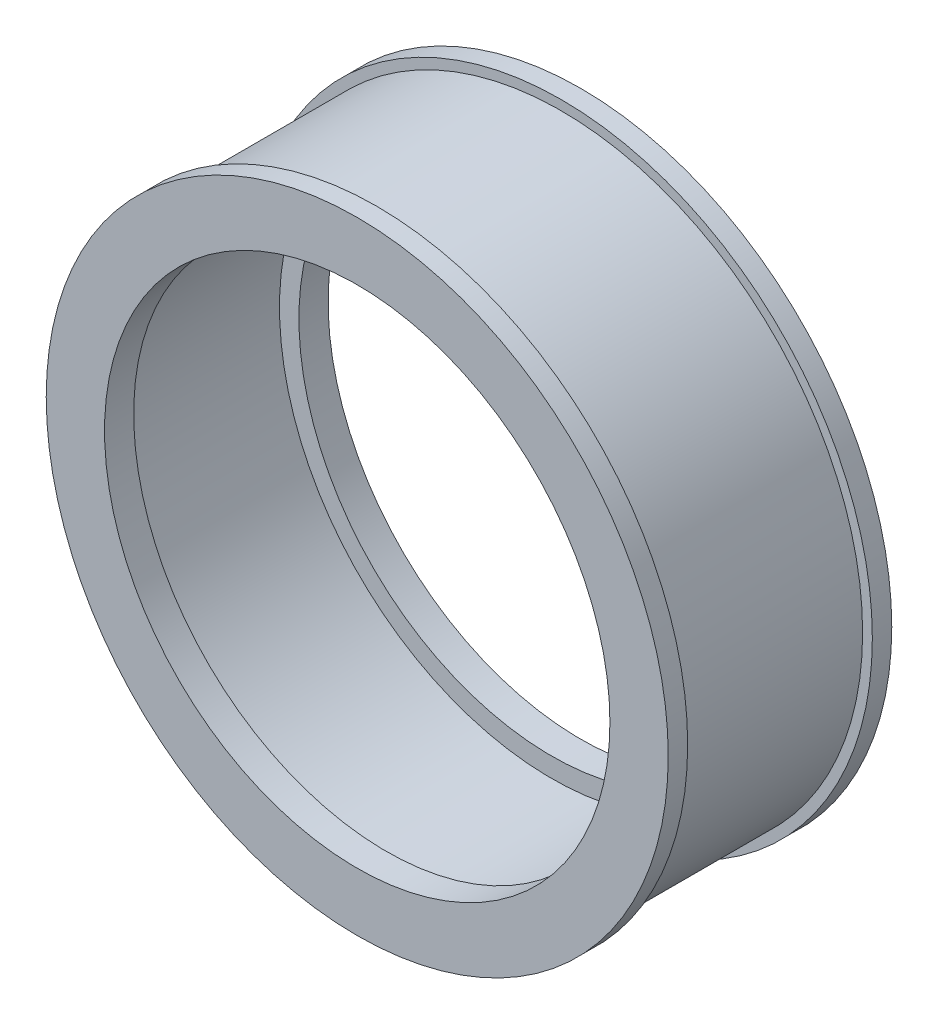
SolidWorks part; units mm, degrees
material "PA Type 6"
ref_plane "Front Plane" through (0, 0, 0) normal (0, 0, 1) x (1, 0, 0)
ref_plane "Top Plane" through (0, 0, 0) normal (0, 1, 0) x (1, 0, 0)
ref_plane "Right Plane" through (0, 0, 0) normal (1, 0, 0) x (0, 0, -1)
sketch "Sketch1" plane through (0, 0, 0) normal (0, 1, 0) x (1, 0, 0)
  line L0 (0, 0) -> (0, 22.7451) construction
  line L1 (26, 11.5) -> (32, 11.5)
  line L2 (28, 8.5) -> (28, -8.5)
  line L3 (26, -11.5) -> (32, -11.5)
  line L5 (31, 9.5) -> (31, -9.5)
  line L8 (31, -9.5) -> (32, -9.5)
  line L9 (32, -11.5) -> (32, -9.5)
  line L11 (28, -8.5) -> (26, -8.5)
  line L12 (31, 9.5) -> (32, 9.5)
  line L13 (32, 11.5) -> (32, 9.5)
  line L15 (26, -11.5) -> (26, -8.5)
  line L20 (28, 8.5) -> (26, 8.5)
  line L21 (26, 11.5) -> (26, 8.5)
  point P4 (28, 0)
  point P14 (31, 0)
  dimension "D2" = 23
  dimension "D3" = 31
  dimension "D4" = 2
  dimension "D5" = 2
  dimension "D6" = 3
  dimension "D7" = 1
  dimension "D8" = 1
  dimension "D9" = 28
  dimension "D10" = 2
  dimension "D11" = 2
revolve "Revolve1" add sketch "Sketch1" angle 360 about L0
